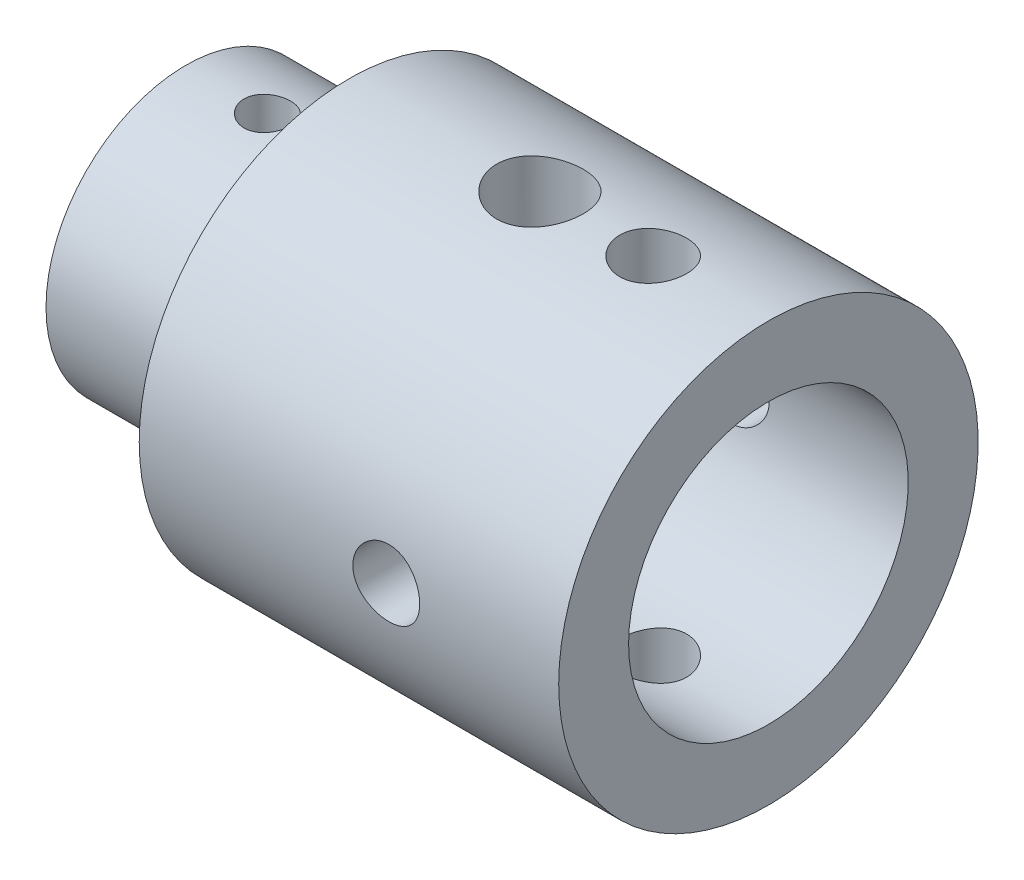
SolidWorks part; units mm, degrees
ref_plane "Alzado" through (0, 0, 0) normal (0, 0, 1) x (1, 0, 0)
ref_plane "Planta" through (0, 0, 0) normal (0, 1, 0) x (1, 0, 0)
ref_plane "Vista lateral" through (0, 0, 0) normal (1, 0, 0) x (0, 0, -1)
sketch "Croquis1" plane through (0, 0, 0) normal (0, 1, 0) x (1, 0, 0)
  line L0 (-57.0801, 0) -> (57.0801, 0) construction
  line L1 (10, 0) -> (10, 6)
  line L2 (10, 6) -> (25, 6)
  line L3 (25, 6) -> (25, 9)
  line L4 (25, 9) -> (7, 9)
  line L5 (0, 6) -> (0, 0)
  line L6 (0, 0) -> (10, 0)
  line L8 (0, 6) -> (7, 6)
  line L9 (7, 6) -> (7, 9)
  point P3 (0, 0)
  dimension "D1" = 12
  dimension "D2" = 3
  dimension "D3" = 15
  dimension "D4" = 3
  dimension "D5" = 0
  dimension "D6" = 6
  dimension "D7" = 7
revolve "Revolución1" add sketch "Croquis1" angle 360 about L0
sketch "Croquis2" plane through (0, 0, 0) normal (-1, 0, 0) x (0, 0, 1)
  line L0 (-1, 0) -> (1, 0) construction
  line L1 (-1, 1.5) -> (1, 1.5)
  line L2 (-1, -1.5) -> (1, -1.5)
  arc A0 (-1, 1.5) -> (-1, -1.5) centre (-1, 0) ccw
  arc A1 (1, -1.5) -> (1, 1.5) centre (1, 0) ccw
  point P2 (0, 0)
  point P8 (2.5, 0)
  point P9 (-2.5, 0)
  dimension "D2" = 5
  dimension "D1" = 3
extrude "Cortar-Extruir1" cut sketch "Croquis2" against normal blind 7
sketch "Croquis3" plane through (0, 0, 0) normal (0, 1, 0) x (1, 0, 0)
  line L0 (0, 6) -> (0, -6) construction
  line L1 (0, -6) -> (7, -6) construction
  circle A0 centre (3.5, 0) radius 1
  dimension "D1" = 2
  dimension "D3" = 6
  dimension "D2" = 3.5
extrude "Cortar-Extruir2" cut sketch "Croquis3" against normal mid plane 14
ref_plane "Plano1" through (0, -9, 0) normal (0, -1, 0) x (-1, 0, 0)
sketch "Croquis4" plane through (0, -9, 0) normal (0, -1, 0) x (-1, 0, 0)
  line L1 (-10, 6) -> (-10, -6) construction
  circle A0 centre (-15.195, 0) radius 1.855
  circle A1 centre (-20.055, 0) radius 1.435
  dimension "D1" = 3.71
  dimension "D2" = 2.87
  dimension "D3" = 5.195
  dimension "D4" = 10.055
extrude "Cortar-Extruir3" cut sketch "Croquis4" against normal blind 28
sketch "Croquis5" plane through (0, 0, 0) normal (0, 0, 1) x (1, 0, 0)
  line L0 (7, 9) -> (7, -9) construction
  circle A0 centre (17.6, 0) radius 1.435
  dimension "D1" = 2.87
  dimension "D2" = 10.6
extrude "Cortar-Extruir4" cut sketch "Croquis5" against normal through all both and the other way through all
